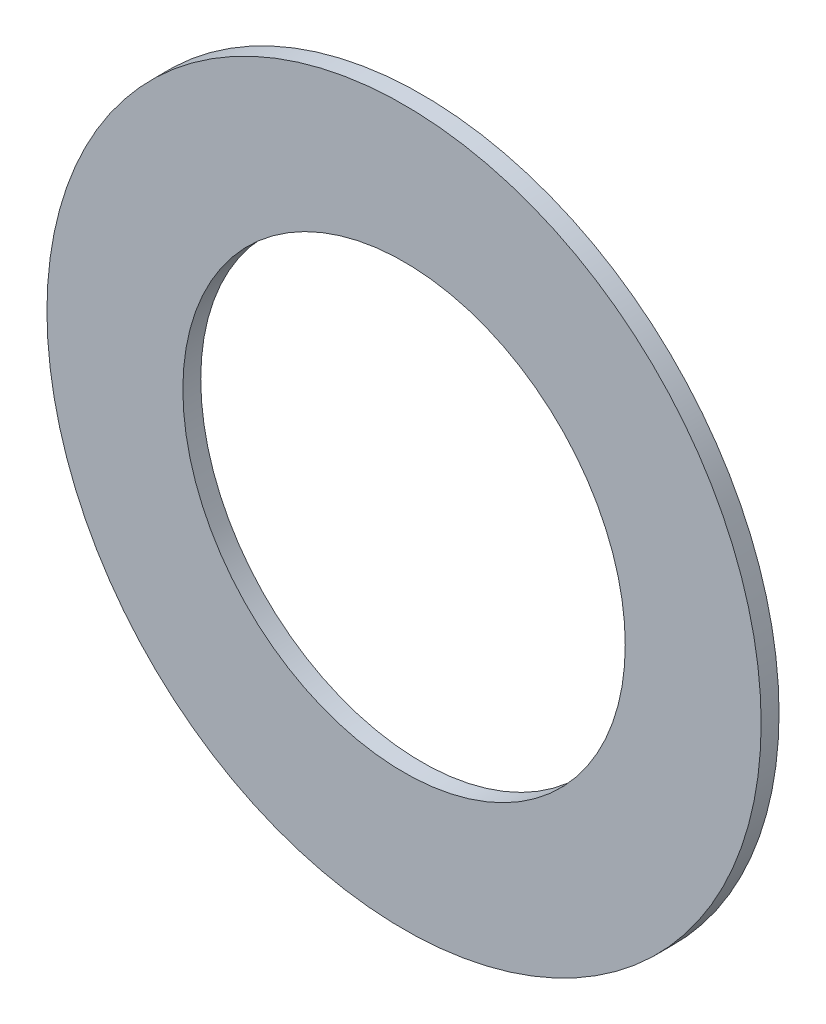
SolidWorks part; units mm, degrees
ref_plane "Front Plane" through (0, 0, 0) normal (0, 0, 1) x (1, 0, 0)
ref_plane "Top Plane" through (0, 0, 0) normal (0, 1, 0) x (1, 0, 0)
ref_plane "Right Plane" through (0, 0, 0) normal (1, 0, 0) x (0, 0, -1)
sketch "Sketch1" plane through (0, 0, 0) normal (0, 0, 1) x (1, 0, 0)
  circle A0 centre (0, 0) radius 63.373
  circle A1 centre (0, 0) radius 39.2557
  dimension "D1" = 78.5114
  dimension "D2" = 126.746
extrude "Boss-Extrude1" add sketch "Sketch1" along normal blind 3.175
equation "\"AIRFRAME_OD\"= 5.15in"
equation "\"AIRFRAME_ID\"= 4.99in"
equation "\"FLAT_T\"= 0.125in"
equation "\"COUPLER_OD\"= 4.998in"
equation "\"COUPLER_ID\"= 4.85in"
equation "\"NOSE_EXP_L\"= 27in"
equation "\"NOSE_SHOULDER_L\"= 5in"
equation "\"MAIN_L\"= 30in"
equation "\"RECO_COUP_L\"= 10in"
equation "\"RECO_SWITCH_L\"= 2in"
equation "\"RECO_ROD_X\"= 3.5in"
equation "\"DROGUE_L\"= 20in"
equation "\"ATS_FORE_COUP_L\"= 5.5in"
equation "\"ATS_AFT_COUP_L\"= 4.5in"
equation "\"ATS_ROD_X\"= 3.75in"
equation "\"LOWER_L\"= 30in"
equation "\"FIN_ROOT\"= 8in"
equation "\"FIN_X\"= 0.75in"
equation "\"FIN_N\"= 4"
equation "\"MOTOR_OD\"= 3.091in"
equation "\"MOTOR_ID\"= 3.00in"
equation "\"MOTOR_L\"= 14in"
equation "\"CR_AFT_X\"= 0.5in"
equation "\"CR_FORE_X\"= 9.25in"
equation "\"D1@Boss-Extrude1\"=\"FLAT_T\""
equation "\"D1@Sketch1\"=\"MOTOR_OD\""
equation "\"D2@Sketch1\"=\"AIRFRAME_ID\""
equation "\"MOTOR_LOWER_X\"= 2in"
